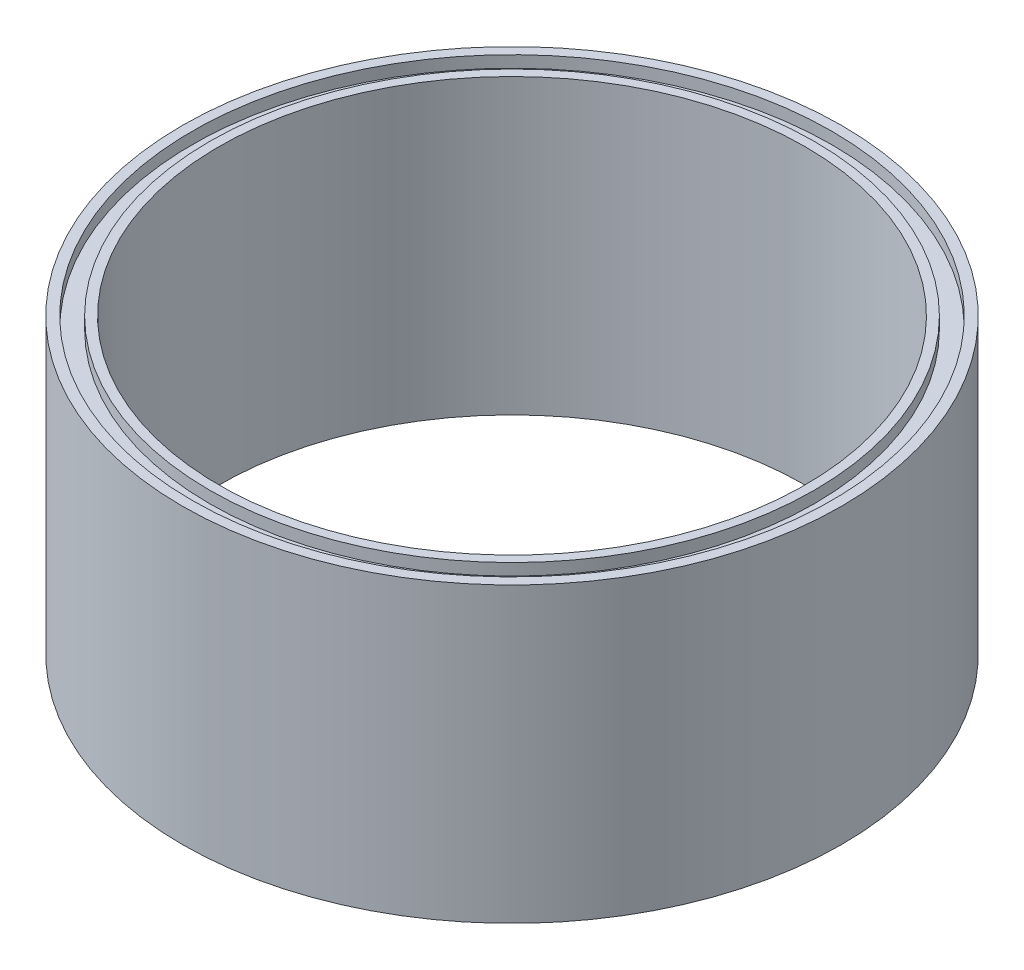
SolidWorks part; units mm, degrees
ref_plane "Front Plane" through (0, 0, 0) normal (0, 0, 1) x (1, 0, 0)
ref_plane "Top Plane" through (0, 0, 0) normal (0, 1, 0) x (1, 0, 0)
ref_plane "Right Plane" through (0, 0, 0) normal (1, 0, 0) x (0, 0, -1)
sketch "Sketch1" plane through (0, 0, 0) normal (0, 0, 1) x (1, 0, 0)
  line L0 (-50.8, 0) -> (-50.8, 50.8)
  line L1 (-50.8, 50.8) -> (-52.3875, 50.8)
  line L2 (-52.3875, 50.8) -> (-52.3875, 48.768)
  line L3 (-52.3875, 48.768) -> (-55.4355, 48.768)
  line L4 (-55.4355, 48.768) -> (-55.4355, 50.8)
  line L5 (-55.4355, 50.8) -> (-57.15, 50.8)
  line L6 (-57.15, 50.8) -> (-57.15, 0)
  line L7 (-57.15, 0) -> (-55.4355, 0)
  line L8 (-55.4355, 0) -> (-55.4355, 2.032)
  line L9 (-55.4355, 2.032) -> (-52.3875, 2.032)
  line L10 (-52.3875, 2.032) -> (-52.3875, 0)
  line L11 (-52.3875, 0) -> (-50.8, 0)
  line L12 (0, 0) -> (0, 26.8079) construction
  dimension "D1" = 2.032
  dimension "D2" = 3.048
  dimension "D3" = 1.5875
  dimension "D4" = 50.8
  dimension "D5" = 2.032
  dimension "D6" = 3.048
  dimension "D7" = 6.35
  dimension "D8" = 1.5875
  dimension "D9" = 50.8
revolve "Revolve1" add sketch "Sketch1" angle 360 about L12
